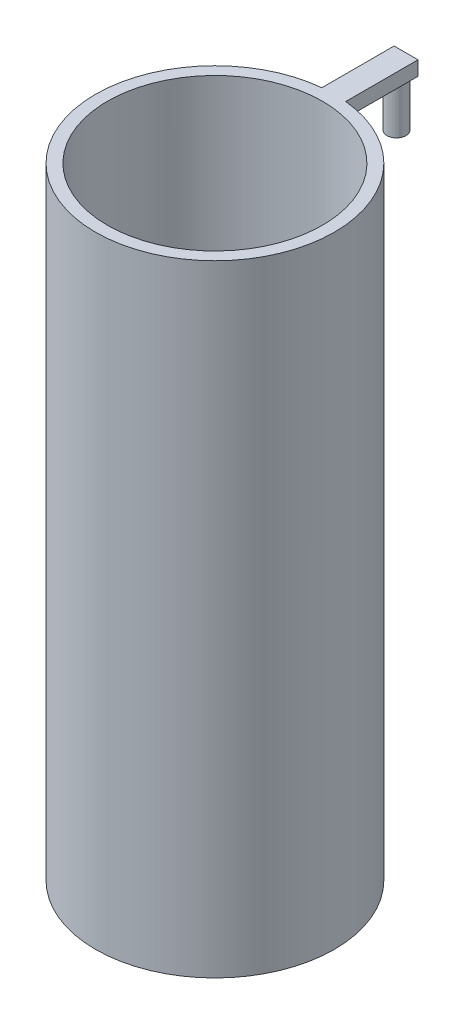
SolidWorks part; units mm, degrees
ref_plane "Front Plane" through (0, 0, 0) normal (0, 0, 1) x (1, 0, 0)
ref_plane "Top Plane" through (0, 0, 0) normal (0, 1, 0) x (1, 0, 0)
ref_plane "Right Plane" through (0, 0, 0) normal (1, 0, 0) x (0, 0, -1)
sketch "Sketch1" plane through (0, 0, 0) normal (0, 1, 0) x (1, 0, 0)
  circle A0 centre (0, 0) radius 22.5
  circle A1 centre (0, 0) radius 25
  dimension "D1" = 45
  dimension "D2" = 50
extrude "Boss-Extrude1" add sketch "Sketch1" along normal blind 130
sketch "Sketch2" plane through (0, 0, 0) normal (0, -1, 0) x (1, 0, 0)
  circle A0 centre (0, 0) radius 25
extrude "Boss-Extrude2" add sketch "Sketch2" against normal blind 5
sketch "Sketch3" plane through (0, 130, 0) normal (0, 1, 0) x (1, 0, 0)
  line L0 (0, 25) -> (0, 40)
  line L2 (-2.5, 40) -> (2.5, 40)
  line L3 (-2.5, 40) -> (-2.5, 24.8747)
  line L4 (-2.5, 24.8747) -> (2.5, 24.8747)
  line L5 (2.5, 40) -> (2.5, 24.8747)
  circle A0 centre (0, 0) radius 25 construction
  circle M6 centre (0, 0) radius 25
  dimension "D1" = 15
  dimension "D2" = 5
extrude "Boss-Extrude3" add sketch "Sketch3" against normal blind 3 contours L2 L3 L0 M6 | L5 L2 L0 M6
sketch "Sketch4" plane through (0, 127, 0) normal (0, -1, 0) x (1, 0, 0)
  line L0 (0, -40) -> (0, -25) construction
  line L1 (-2.5, -40) -> (2.5, -40) construction
  circle A0 centre (0, -38) radius 2
  arc A1 (-2.5, -24.8747) -> (2.5, -24.8747) centre (0, 0) ccw construction
  dimension "D1" = 4
  dimension "D2" = 13
extrude "Boss-Extrude4" add sketch "Sketch4" along normal blind 10
